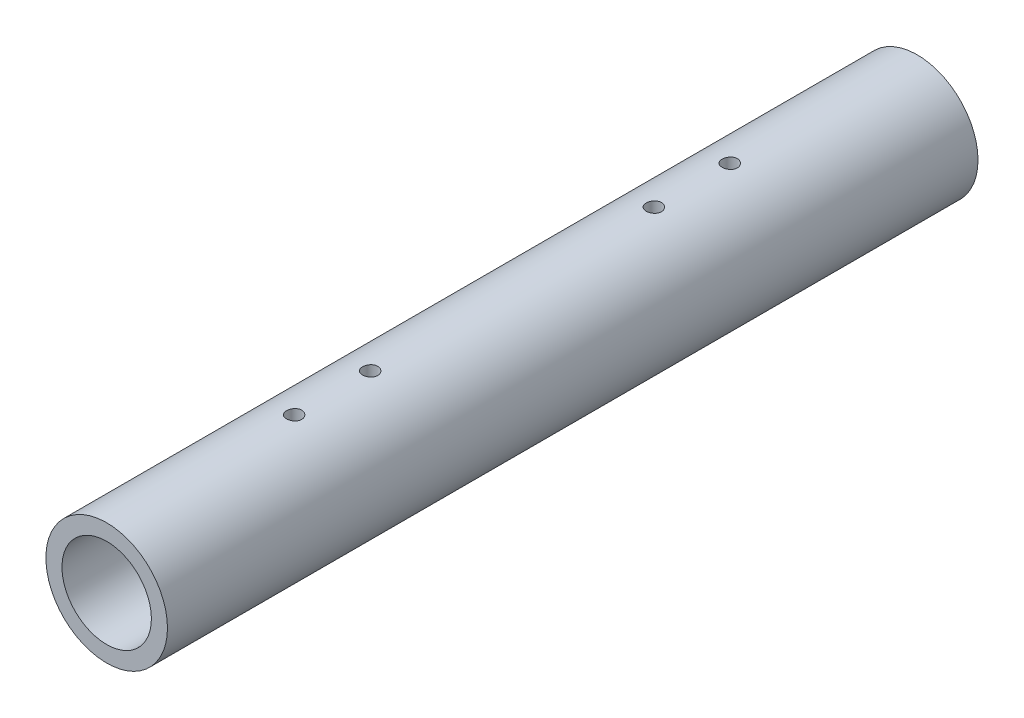
SolidWorks part; units mm, degrees
ref_plane "Front Plane" through (0, 0, 0) normal (0, 0, 1) x (1, 0, 0)
ref_plane "Top Plane" through (0, 0, 0) normal (0, 1, 0) x (1, 0, 0)
ref_plane "Right Plane" through (0, 0, 0) normal (1, 0, 0) x (0, 0, -1)
sketch "Sketch1" plane through (0, 0, 0) normal (0, 0, 1) x (1, 0, 0)
  circle A0 centre (0, 0) radius 12
  dimension "D1" = 24
extrude "Boss-Extrude1" add sketch "Sketch1" along normal mid plane 160
shell "Shell1" thickness 3.175
sketch "Sketch3" plane through (0, 0, 0) normal (0, 1, 0) x (1, 0, 0)
  line L0 (0, 0) -> (0, 28) construction
  line L1 (0, 0) -> (0, -28) construction
  line L2 (0, 28) -> (0, 43) construction
  line L3 (0, -28) -> (0, -43) construction
  circle A0 centre (0, 28) radius 1.5
  circle A1 centre (0, -28) radius 1.5
  circle A2 centre (0, -43) radius 1.5
  circle A3 centre (0, 43) radius 1.5
  dimension "D2" = 3
  dimension "D1" = 28
  dimension "D3" = 15
extrude "Cut-Extrude1" cut sketch "Sketch3" against normal through all both and the other way through all
equation "\"tubeOutDiameter\" = 35mm"
equation "\"wheelShaftDiameter\"= 12mm"
equation "\"wheelThickness\"= 135mm"
equation "\"BearingDiameter\"= 20mm"
equation "\"BearingThickness\"= 10mm"
equation "\"frontShaftDiameter\"= 20mm"
equation "\"D1@Sketch1\"=\"wheelShaftDiameter\"*2"
